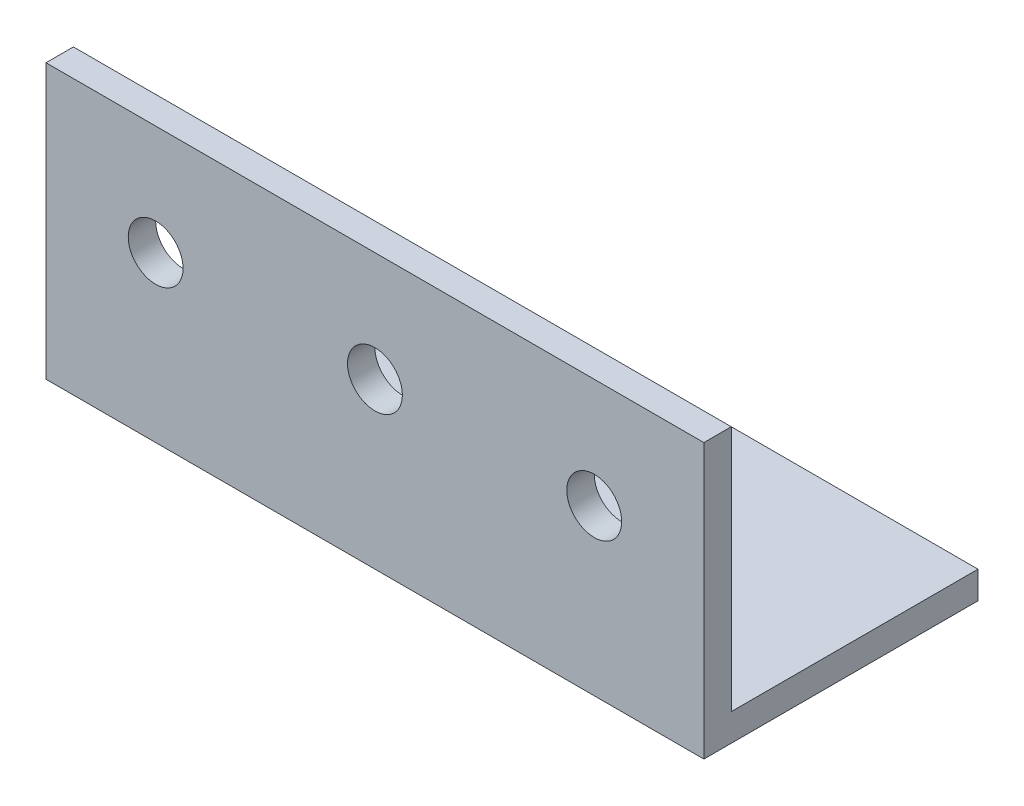
SolidWorks part; units mm, degrees
material "6061-T6 (SS)"
ref_plane "Front Plane" through (0, 0, 0) normal (0, 0, 1) x (1, 0, 0)
ref_plane "Top Plane" through (0, 0, 0) normal (0, 1, 0) x (1, 0, 0)
ref_plane "Right Plane" through (0, 0, 0) normal (1, 0, 0) x (0, 0, -1)
sketch "Sketch1" plane through (0, 0, 0) normal (1, 0, 0) x (0, 0, -1)
  line L1 (0, 0) -> (-3.175, 0)
  line L2 (0, 0) -> (0, 28.575)
  line L3 (0, 28.575) -> (-3.175, 28.575)
  line L4 (-3.175, 0) -> (-3.175, 28.575)
  line L5 (-3.175, 0) -> (28.575, 0)
  line L6 (-3.175, 0) -> (-3.175, -3.175)
  line L7 (-3.175, -3.175) -> (28.575, -3.175)
  line L8 (28.575, 0) -> (28.575, -3.175)
  dimension "D1" = 3.175
  dimension "D2" = 3.175
  dimension "D3" = 31.75
  dimension "D4" = 31.75
extrude "Boss-Extrude1" add sketch "Sketch1" along normal blind 76.2 contours L4 L1 L2 L3 | L8 L5 L1 L6 L7
sketch "Sketch2" plane through (0, 0, 0) normal (0, 0, -1) x (-1, 0, 0)
  line L0 (-76.2, -3.175) -> (0, -3.175) construction
  line L1 (-76.2, 15.875) -> (0, 15.875) construction
  line L2 (-76.2, 0) -> (-76.2, 28.575) construction
  line L3 (0, 0) -> (0, 28.575) construction
  circle A0 centre (-38.1, 15.875) radius 3.175
  circle A1 centre (-63.5, 15.875) radius 3.175
  circle A2 centre (-12.7, 15.875) radius 3.175
  point P14 (-34.5705, 15.875)
  point P15 (-38.1, 15.875)
  dimension "D2" = 6.35
  dimension "D1" = 19.05
  dimension "D3" = 25.4
  dimension "D4" = 25.4
extrude "Cut-Extrude1" cut sketch "Sketch2" against normal blind 76.2
